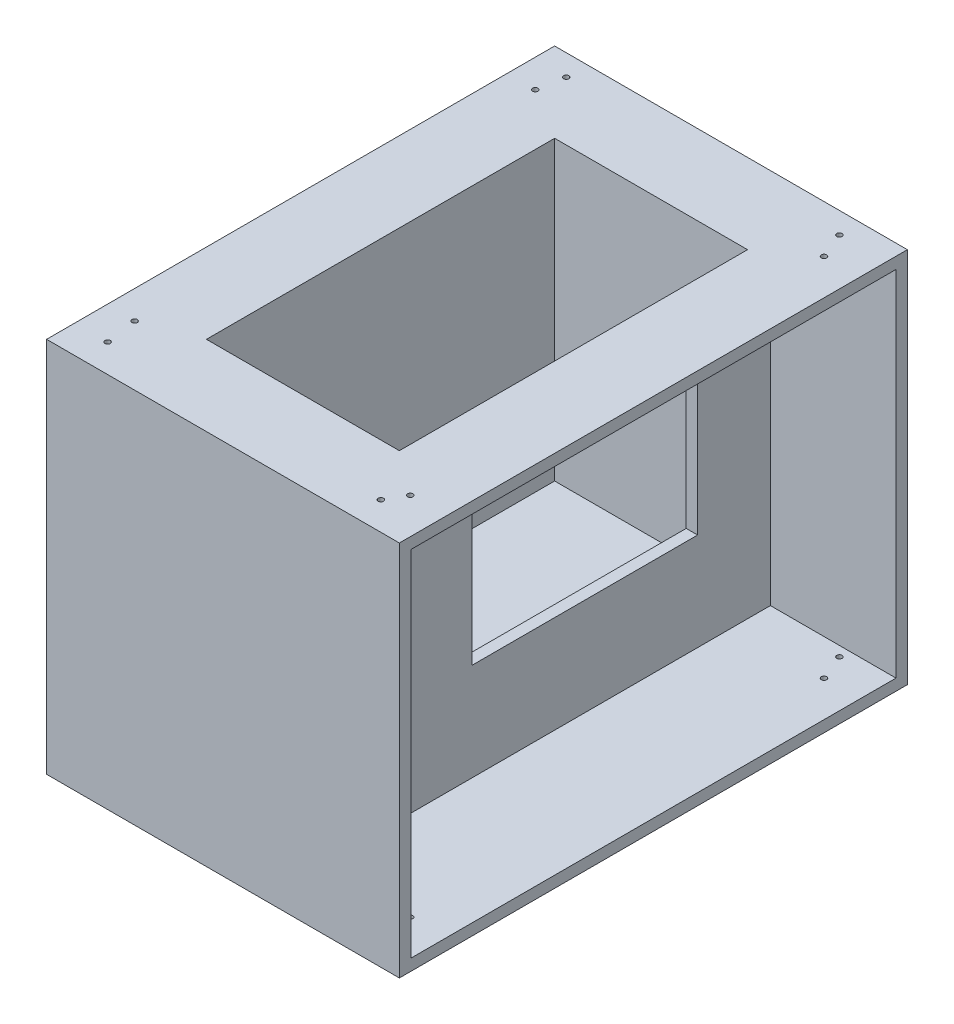
SolidWorks part; units mm, degrees
ref_plane "Front Plane" through (0, 0, 0) normal (0, 0, 1) x (1, 0, 0)
ref_plane "Top Plane" through (0, 0, 0) normal (0, 1, 0) x (1, 0, 0)
ref_plane "Right Plane" through (0, 0, 0) normal (1, 0, 0) x (0, 0, -1)
sketch "Sketch1" plane through (0, 0, 0) normal (0, 1, 0) x (1, 0, 0)
  line L1 (39.243, -56.515) -> (-39.243, -56.515)
  line L2 (39.243, -56.515) -> (39.243, 56.515)
  line L3 (39.243, 56.515) -> (-39.243, 56.515)
  line L4 (-39.243, -56.515) -> (-39.243, 56.515)
  line L5 (39.243, -56.515) -> (-39.243, 56.515) construction
  line L6 (39.243, 56.515) -> (-39.243, -56.515) construction
  point P0 (0, 0)
  dimension "D1" = 113.03
  dimension "D2" = 78.486
extrude "Boss-Extrude1" add sketch "Sketch1" along normal blind 68.326 and the other way blind 15.494
shell "Shell1" thickness 17.78
shell "Shell5" thickness 2.54
sketch "Sketch2" plane through (24.003, 0, 0) normal (1, 0, 0) x (0, 0, -1)
  line L1 (25.0831, 21.4392) -> (-25.0831, 21.4392)
  line L2 (25.0831, 21.4392) -> (25.0831, 55.4142)
  line L3 (25.0831, 55.4142) -> (-25.0831, 55.4142)
  line L4 (-25.0831, 21.4392) -> (-25.0831, 55.4142)
  line L5 (25.0831, 21.4392) -> (-25.0831, 55.4142) construction
  line L6 (25.0831, 55.4142) -> (-25.0831, 21.4392) construction
  point P0 (0, 38.4267)
  dimension "D1" = 33.975
  dimension "D2" = 50.1661
extrude "Cut-Extrude1" cut sketch "Sketch2" against normal blind 12.446
hole_wizard "#0-80 Tapped Hole1" positions "Sketch3" profile "Sketch4" tap size "#0-80" standard "ANSI Inch" end condition through all
sketch "Sketch3" plane through (0, 68.326, 0) normal (0, 1, 0) x (1, 0, 0)
  point P0 (-31.9452, 51.7821)
  point P2 (-32.9757, 45.9427)
  point P4 (28.8537, 51.7821)
  point P6 (31.2582, 45.9427)
  point P8 (31.2582, -46.1144)
  point P10 (28.8537, -50.2364)
  point P12 (-31.9452, -50.2364)
  point P14 (-32.9757, -43.1947)
sketch "Sketch4" plane through (-31.9452, 68.326, -51.7821) normal (1, 0, 0) x (0, 0, 1)
  line L0 (0, 0) -> (0, 83.82)
  line L1 (0, 83.82) -> (0.5956, 83.82)
  line L2 (0.5956, 83.82) -> (0.5956, 0)
  line L5 (0.5956, 0) -> (0, 0)
  line L11 (0, -6.35) -> (0, 107.95) construction
  dimension "Thru Tap Drill Dia." = 1.1913
  dimension "Thru Tap Drill Depth" = 83.82
cosmetic thread "Hole Thread1" parameters "D2"=1.524
cosmetic thread "Hole Thread2" parameters "D2"=1.524
cosmetic thread "Hole Thread3" parameters "D2"=1.524
cosmetic thread "Hole Thread4" parameters "D2"=1.524
cosmetic thread "Hole Thread5" parameters "D2"=1.524
cosmetic thread "Hole Thread6" parameters "D2"=1.524
cosmetic thread "Hole Thread7" parameters "D2"=1.524
cosmetic thread "Hole Thread8" parameters "D2"=1.524
